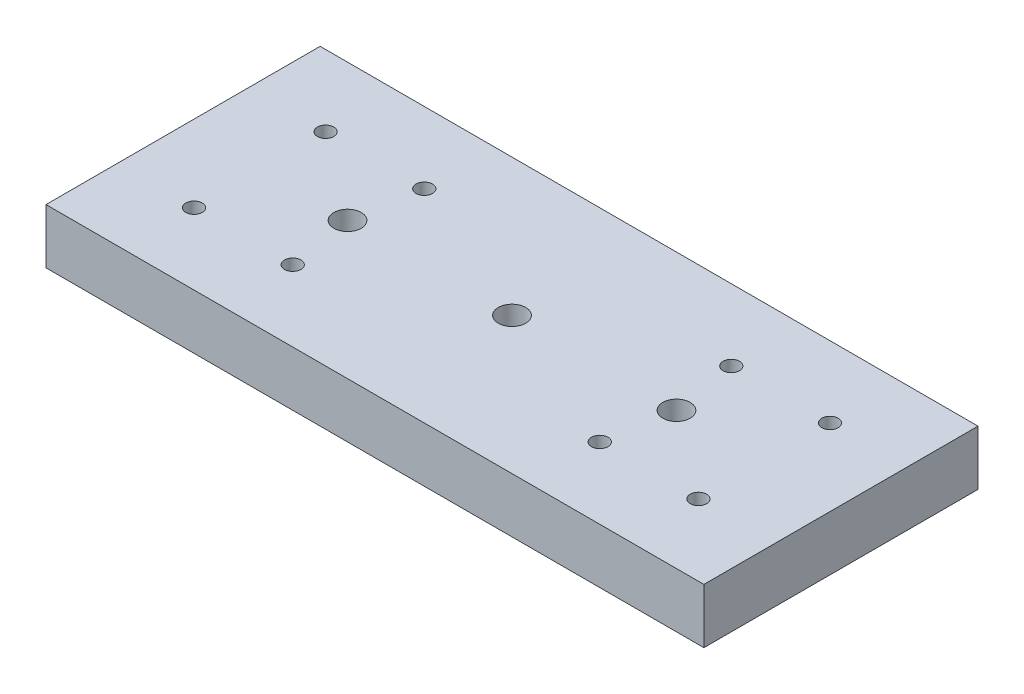
SolidWorks part; units mm, degrees
ref_plane "Front Plane" through (0, 0, 0) normal (0, 0, 1) x (1, 0, 0)
ref_plane "Top Plane" through (0, 0, 0) normal (0, 1, 0) x (1, 0, 0)
ref_plane "Right Plane" through (0, 0, 0) normal (1, 0, 0) x (0, 0, -1)
sketch "Sketch1" plane through (0, 0, 0) normal (0, 1, 0) x (1, 0, 0)
  line L1 (60, -25) -> (-60, -25)
  line L2 (60, -25) -> (60, 25)
  line L3 (60, 25) -> (-60, 25)
  line L4 (-60, -25) -> (-60, 25)
  line L5 (60, -25) -> (-60, 25) construction
  line L6 (60, 25) -> (-60, -25) construction
  point P0 (0, 0)
  dimension "D1" = 50
  dimension "D2" = 120
extrude "Boss-Extrude1" add sketch "Sketch1" along normal blind 10
sketch "Sketch2" plane through (0, 10, 0) normal (0, 1, 0) x (1, 0, 0)
  circle A1 centre (28, -12) radius 1.5
  circle A2 centre (28, -12) radius 1.5
  circle A3 centre (28, 12) radius 1.5
  circle A4 centre (28, 12) radius 1.5
  circle A5 centre (46, -12) radius 1.5
  circle A6 centre (46, -12) radius 1.5
  circle A7 centre (46, 12) radius 1.5
  circle A8 centre (46, 12) radius 1.5
  circle A9 centre (-46, -12) radius 1.5
  circle A10 centre (-46, -12) radius 1.5
  circle A11 centre (-46, 12) radius 1.5
  circle A12 centre (-46, 12) radius 1.5
  circle A13 centre (-28, -12) radius 1.5
  circle A14 centre (-28, -12) radius 1.5
  circle A15 centre (-28, 12) radius 1.5
  circle A16 centre (-28, 12) radius 1.5
  dimension "D1" = 0
  dimension "D2" = 0
  dimension "D3" = 0
  dimension "D4" = 0
  dimension "D5" = 0
  dimension "D6" = 0
  dimension "D7" = 0
  dimension "D8" = 0
extrude "Cut-Extrude1" cut sketch "Sketch2" against normal through all
sketch "Sketch3" plane through (0, 0, 0) normal (0, -1, 0) x (1, 0, 0)
  line L2 (60, 25) -> (60, -25) construction
  circle A0 centre (0, 0) radius 2.5
  circle A1 centre (30, 0) radius 2.5
  circle A2 centre (-30, 0) radius 2.5
  point P7 (0, 0)
  point P12 (0, 0)
  point P16 (-28.67, 0.4585)
  dimension "D1" = 5
  dimension "D2" = 30
  dimension "D3" = 30
  dimension "D5" = 30
extrude "Cut-Extrude2" cut sketch "Sketch3" against normal through all
sketch "Sketch4" plane through (0, 0, 0) normal (0, -1, 0) x (1, 0, 0)
  circle A0 centre (30, 0) radius 4.25
  circle A1 centre (0, 0) radius 4.25
  circle A2 centre (-30, 0) radius 4.25
  point P9 (0, 0)
  dimension "D1" = 8.5
extrude "Cut-Extrude3" cut sketch "Sketch4" against normal blind 5
